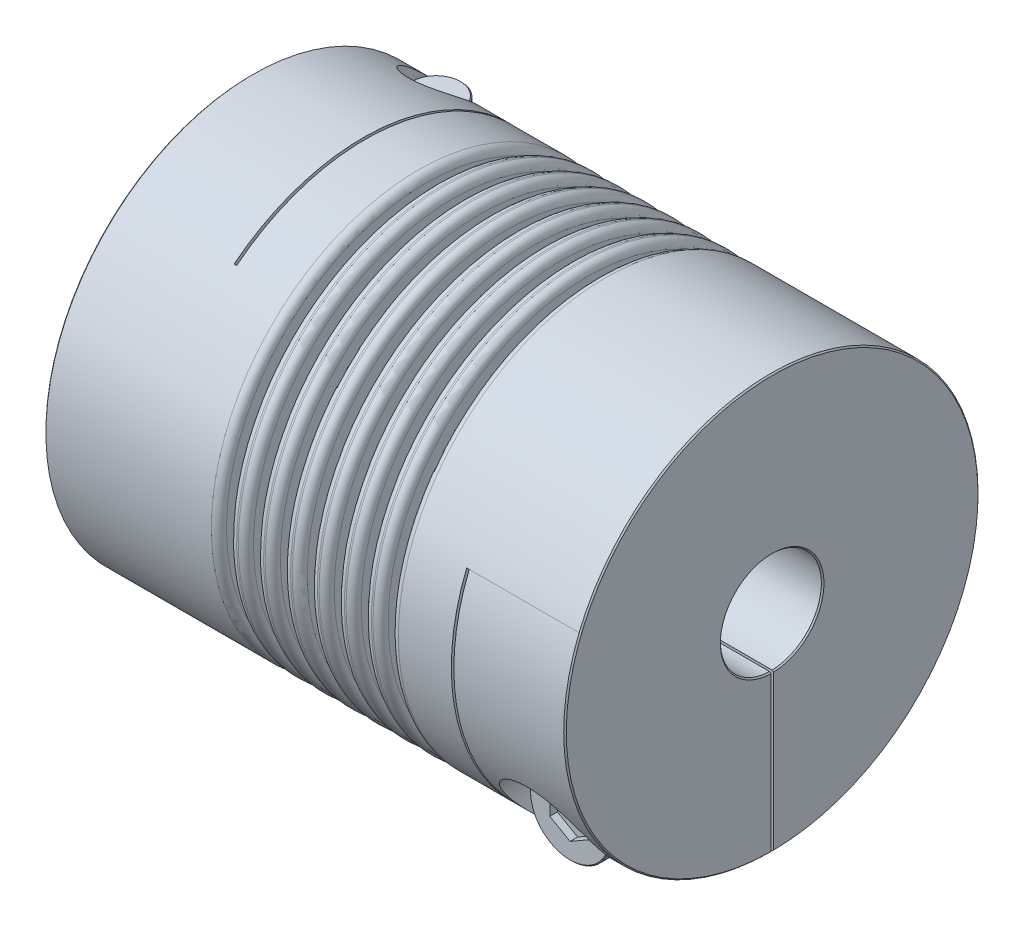
SolidWorks part; units mm, degrees
ref_plane "Front Plane" through (0, 0, 0) normal (0, 0, 1) x (1, 0, 0)
ref_plane "Top Plane" through (0, 0, 0) normal (0, 1, 0) x (1, 0, 0)
ref_plane "Right Plane" through (0, 0, 0) normal (1, 0, 0) x (0, 0, -1)
sketch "Sketch1" plane through (0, 0, 0) normal (1, 0, 0) x (0, 0, -1)
  circle A0 centre (0, 0) radius 41
  dimension "dim D" = 82
extrude "Boss-Extrude1" add sketch "Sketch1" along normal mid plane 103
sketch "Sketch2" plane through (51.5, 0, 0) normal (1, 0, 0) x (0, 0, -1)
  circle A0 centre (0, 0) radius 10
  dimension "dim D1" = 20
extrude "Cut-Extrude1" cut sketch "Sketch2" against normal through all
chamfer "Chamfer1" distance 0.254 angle 45 4 edges at (-51.5, 0, -10) (-51.5, 0, -41) (51.5, 0, -41) (51.5, 0, -10)
ref_plane "Plane2" through (0, -41, 0) normal (0, -1, 0) x (1, 0, 0)
ref_plane "F" through (-40.5, 0, 0) normal (-1, 0, 0) x (0, 0, 1)
sketch "Sketch4" plane through (0, -41, 0) normal (0, -1, 0) x (1, 0, 0)
  line L0 (-51.246, -41) -> (51.246, -41) construction
  line L1 (-29.5, -41) -> (-29, -41)
  line L2 (-29.5, -41) -> (-29.5, 25.5)
  line L3 (-29.5, 25.5) -> (-29, 25.5)
  line L4 (-29, -41) -> (-29, 25.5)
  line L5 (-29.5, 10) -> (-29.5, 41) construction
  line L6 (51.246, 10) -> (-51.246, 10) construction
  line L7 (51.246, 41) -> (-51.246, 41) construction
  line L10 (-29.5, 25.5) -> (-51.5, 25.5) construction
  line L11 (-51.5, 40.746) -> (-51.5, -40.746) construction
  line L12 (-40.5, 10.2256) -> (-40.5, -10.2256) construction
  point P16 (-40.5, 25.5)
  dimension "D1" = 0.5
extrude "Cut-Extrude2" cut sketch "Sketch4" against normal through all
ref_plane "Plane4" through (0, 0, -41) normal (0, 0, -1) x (-1, 0, 0)
sketch "Sketch7" plane through (0, 0, -41) normal (0, 0, -1) x (-1, 0, 0)
  line L1 (-29, -41) -> (-29.5, -41)
  line L2 (-29.5, -41) -> (-29.5, 15.5)
  line L3 (-29.5, 15.5) -> (-29, 15.5)
  line L4 (-29, -41) -> (-29, 15.5)
  line L5 (51.5, 8.6487) -> (40.5, 8.6487) construction
  line L7 (-10.505, -41) -> (10.505, -41) construction
  line L8 (-51.246, -10) -> (29, -10) construction
  line L9 (51.5, -40.746) -> (51.5, 40.746) construction
  line L10 (-51.246, -10) -> (29, -10) construction
  line L11 (29, 32.1053) -> (29.5, 32.1053) construction
  line L12 (-29.5, 15.5) -> (-29.5, -41) construction
  line L14 (-51.246, -10) -> (29, -10) construction
  line L16 (-51.246, -10) -> (29, -10) construction
  line L17 (29.5, -41) -> (51.246, -41) construction
  line L18 (40.5, -10.2256) -> (40.5, 10.2256) construction
  line L19 (-51.246, -41) -> (-51.246, 41) construction
  line L20 (-51.5, 15.5) -> (-40.5, 15.5) construction
  line L21 (-51.5, 40.746) -> (-51.5, -40.746) construction
  line L22 (-40.5, 15.5) -> (-29.5, 15.5) construction
  line L23 (-51.246, -41) -> (-51.246, 41) construction
  line L24 (-51.246, -10) -> (-51.246, 41) construction
  line L25 (-51.246, -10) -> (29, -10) construction
  point P23 (-29.5, 15.5)
  point P33 (-51.246, 15.5)
extrude "Cut-Extrude3" cut sketch "Sketch7" against normal through all
sketch "Sketch8" plane through (0, 0, 0) normal (0, 1, 0) x (1, 0, 0)
  line L0 (-29.5, -25.5) -> (-29.5, 41) construction
  line L1 (-51.5, 41) -> (-29.5, 41)
  line L2 (-51.5, 41) -> (-51.5, 0)
  line L3 (-51.5, 0) -> (-29.5, 0)
  line L4 (-29.5, 41) -> (-29.5, 0)
  line L5 (10.505, 41) -> (-10.505, 41) construction
  line L6 (-51.5, 40.746) -> (-51.5, -40.746) construction
extrude "Cut-Extrude5" cut sketch "Sketch8" against normal mid plane 0.5
sketch "Sketch13" plane through (0, 0, 0) normal (0, 0, 1) x (1, 0, 0)
  line L0 (51.5, -40.746) -> (51.5, 40.746) construction
  line L1 (29.5, -41) -> (51.5, -41)
  line L2 (29.5, -41) -> (29.5, 0)
  line L3 (29.5, 0) -> (51.5, 0)
  line L4 (51.5, -41) -> (51.5, 0)
extrude "Cut-Extrude6" cut sketch "Sketch13" against normal mid plane 0.5
hole_wizard "CBORE for M10 SHCS2" positions "Sketch12" profile "Sketch11" counterbore size "M10" standard "Ansi Metric" end condition through all
sketch "Sketch12" plane through (0, -41, 0) normal (0, -1, 0) x (1, 0, 0)
  line L0 (-40.5, 10.2256) -> (-40.5, -10.2256) construction
  line L1 (-29.5, -9.9969) -> (-29.5, -40.9992) construction
  line L2 (-29.5, -9.9969) -> (-29.5, -40.9992)
  line L3 (-29.5, -25.4981) -> (-40.5, -25.4981) construction
  point P0 (-40.5, -25.4981)
sketch "Sketch11" plane through (-40.5, -41, -25.4981) normal (1, 0, 0) x (0, 0, -1)
  line L0 (0, 0) -> (0, 82)
  line L1 (0, 82) -> (5.5, 82)
  line L3 (5.5, 82) -> (5.5, 20)
  line L4 (5.5, 20) -> (9, 20)
  line L5 (9, 20) -> (9, 0)
  line L7 (9, 0) -> (0, 0)
  line L11 (0, -6.35) -> (0, 107.95) construction
  dimension "Thru Hole Dia." = 11
  dimension "Thru Hole Depth" = 82
  dimension "C'Bore Dia." = 18
  dimension "C'Bore Depth" = 20
ref_plane "Plane5" through (0, 0, 41) normal (0, 0, 1) x (1, 0, 0)
hole_wizard "CBORE for M10 SHCS1" positions "Sketch15" profile "Sketch14" counterbore size "M10" standard "Ansi Metric" end condition through all
sketch "Sketch15" plane through (0, 0, 41) normal (0, 0, 1) x (1, 0, 0)
  line L0 (-49.5, -21) -> (-31.5, -21) construction
  line L1 (-49.5, -21) -> (-31.5, -21)
  line L5 (0, 0) -> (0, 41) construction
  line L6 (-29.5, 41) -> (-51.246, 41) construction
  line L8 (49.5, -21) -> (31.5, -21)
  line L9 (40.5, -21) -> (40.5, -25.4981) construction
  line L11 (40.5, -40.9992) -> (40.5, -9.9969) construction
  line L12 (51.246, -40.9992) -> (29.5, -40.9992) construction
  line L13 (29.5, -9.9969) -> (51.246, -9.9969) construction
  point P0 (40.5, -25.4981)
sketch "Sketch14" plane through (40.5, -25.4981, 41) normal (1, 0, 0) x (0, -1, 0)
  line L0 (0, 0) -> (0, 82)
  line L1 (0, 82) -> (5.5, 82)
  line L3 (5.5, 82) -> (5.5, 22)
  line L4 (5.5, 22) -> (9, 22)
  line L5 (9, 22) -> (9, 0)
  line L7 (9, 0) -> (0, 0)
  line L11 (0, -6.35) -> (0, 107.95) construction
  dimension "Thru Hole Dia." = 11
  dimension "Thru Hole Depth" = 82
  dimension "C'Bore Dia." = 18
  dimension "C'Bore Depth" = 22
sketch "Sketch16" plane through (0, 0, 19) normal (0, 0, 1) x (1, 0, 0)
  circle A0 centre (40.5, -25.4981) radius 8
  dimension "screw dia" = 16
extrude "Boss-Extrude2" add sketch "Sketch16" along normal blind 10 separate body
sketch "Sketch17" plane through (0, 0, 19) normal (0, 0, -1) x (-1, 0, 0)
  circle A0 centre (-40.5, -25.4981) radius 5
  dimension "D1" = 10
extrude "Boss-Extrude3" add sketch "Sketch17" along normal blind 49
chamfer "Chamfer2" distance 0.2 angle 45 3 edges at (35.5, -25.4981, -30) (48.5, -25.4981, 19) (48.5, -25.4981, 29)
sketch "Sketch18" plane through (0, 0, 29) normal (0, 0, 1) x (1, 0, 0)
  line L1 (40.5, -30.1169) -> (44.5, -27.8075)
  line L2 (44.5, -27.8075) -> (44.5, -23.1887)
  line L3 (44.5, -23.1887) -> (40.5, -20.8793)
  line L4 (40.5, -20.8793) -> (36.5, -23.1887)
  line L5 (36.5, -23.1887) -> (36.5, -27.8075)
  line L6 (36.5, -27.8075) -> (40.5, -30.1169)
  circle A0 centre (40.5, -25.4981) radius 4 construction
  dimension "hex" = 8
extrude "Cut-Extrude7" cut sketch "Sketch18" against normal blind 1.5
mirror "Mirror1" about plane through (0, 0, 0) normal (1, 0, 0) of bodies 121
pattern_circular "CirPattern1" count 2 every 90 about axis through (0, 0, 0) along (1, 0, 0) of bodies 122 117
delete or keep bodies "Body-Delete1" type delete bodies bodies 122
sketch "Sketch19" plane through (0, 0, 0) normal (0, 0, 1) x (1, 0, 0)
  line L0 (-51.5, -28) -> (51.5, -28) construction
  line L1 (-51.5, 40.746) -> (-51.5, -40.746) construction
  line L2 (51.5, -40.7452) -> (51.5, 40.746) construction
  line L3 (0, 0) -> (0, -28) construction
  line L4 (0, 0) -> (0, 28) construction
  line L5 (51.246, 41) -> (-29, 41) construction
  line L6 (-1, 41) -> (1, 41)
  line L7 (-1, 41) -> (-1, 28)
  line L8 (-1, 28) -> (1, 28)
  line L9 (1, 41) -> (1, 28)
  line L10 (4.3333, 41) -> (6.3333, 41)
  line L11 (4.3333, 41) -> (4.3333, 28)
  line L12 (4.3333, 28) -> (6.3333, 28)
  line L13 (6.3333, 41) -> (6.3333, 28)
  line L14 (9.6667, 41) -> (11.6667, 41)
  line L15 (9.6667, 41) -> (9.6667, 28)
  line L16 (9.6667, 28) -> (11.6667, 28)
  line L17 (11.6667, 41) -> (11.6667, 28)
  line L18 (15, 41) -> (17, 41)
  line L19 (15, 41) -> (15, 28)
  line L20 (15, 28) -> (17, 28)
  line L21 (17, 41) -> (17, 28)
  line L22 (-17, 41) -> (-17, 28)
  line L23 (-15, 28) -> (-17, 28)
  line L24 (-15, 41) -> (-15, 28)
  line L25 (-15, 41) -> (-17, 41)
  line L26 (-11.6667, 41) -> (-11.6667, 28)
  line L27 (-9.6667, 28) -> (-11.6667, 28)
  line L28 (-9.6667, 41) -> (-9.6667, 28)
  line L29 (-9.6667, 41) -> (-11.6667, 41)
  line L30 (-6.3333, 41) -> (-6.3333, 28)
  line L31 (-4.3333, 28) -> (-6.3333, 28)
  line L32 (-4.3333, 41) -> (-4.3333, 28)
  line L33 (-4.3333, 41) -> (-6.3333, 41)
  line L34 (0, 0) -> (-51.5, 0) construction
  dimension "D1" = 2
  dimension "Dim E" = 56
  dimension "Dim L1" = 34.5
  dimension "D2" = 4
revolve "Cut-Revolve1" cut sketch "Sketch19" angle 360 about L34
fillet "Fillet1" radius 1.5 14 edges at (-15, 41, 0) (-11.6667, 41, 0) (-9.6667, 41, 0) (-6.3333, 41, 0) (-1, 41, 0) (-4.3333, 41, 0) (1, 41, 0) (4.3333, 41, 0) (6.3333, 41, 0) (9.6667, 41, 0) (11.6667, 41, 0) (15, 41, 0) (17, 41, 0) (-17, 41, 0)
fillet "Fillet2" radius 0.1 14 edges at (15, 28, 0) (17, 28, 0) (9.6667, 28, 0) (11.6667, 28, 0) (4.3333, 28, 0) (6.3333, 28, 0) (-1, 28, 0) (1, 28, 0) (-6.3333, 28, 0) (-4.3333, 28, 0) (-11.6667, 28, 0) (-9.6667, 28, 0) (-17, 28, 0) (-15, 28, 0)
